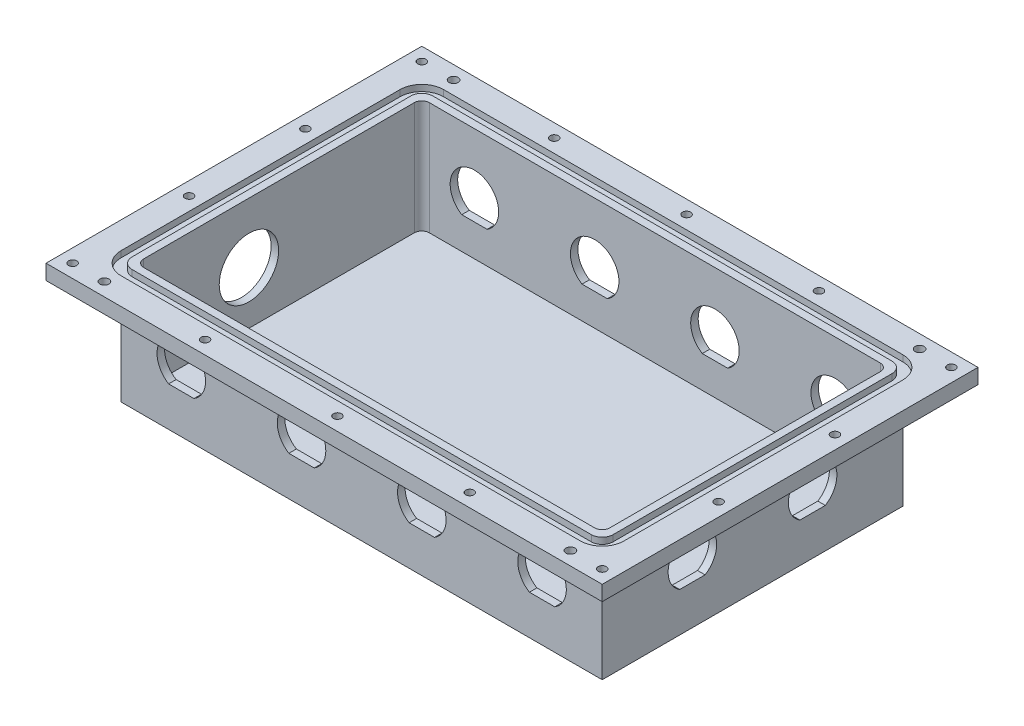
SolidWorks part; units mm, degrees
material "1060 Alloy"
ref_plane "Front Plane" through (0, 0, 0) normal (0, 0, 1) x (1, 0, 0)
ref_plane "Top Plane" through (0, 0, 0) normal (0, 1, 0) x (1, 0, 0)
ref_plane "Right Plane" through (0, 0, 0) normal (1, 0, 0) x (0, 0, -1)
sketch "Sketch1" plane through (0, 0, 0) normal (0, 1, 0) x (1, 0, 0)
  line L1 (101.6, -63.5) -> (-101.6, -63.5)
  line L2 (101.6, -63.5) -> (101.6, 63.5)
  line L3 (101.6, 63.5) -> (-101.6, 63.5)
  line L4 (-101.6, -63.5) -> (-101.6, 63.5)
  line L5 (101.6, -63.5) -> (-101.6, 63.5) construction
  line L6 (101.6, 63.5) -> (-101.6, -63.5) construction
  point P0 (0, 0)
  dimension "D1" = 127
  dimension "D2" = 203.2
extrude "Boss-Extrude1" add sketch "Sketch1" along normal blind 50.8
sketch "Sketch2" plane through (0, 50.8, 0) normal (0, 1, 0) x (1, 0, 0)
  line L8 (-98.425, 60.325) -> (-98.425, -60.325)
  line L9 (98.425, 60.325) -> (-98.425, 60.325)
  line L10 (98.425, -60.325) -> (98.425, 60.325)
  line L11 (-98.425, -60.325) -> (98.425, -60.325)
  line L12 (-98.425, 60.325) -> (-98.425, -60.325)
  line L13 (98.425, 60.325) -> (-98.425, 60.325)
  line L14 (98.425, -60.325) -> (98.425, 60.325)
  line L15 (-98.425, -60.325) -> (98.425, -60.325)
  dimension "D1" = 3.175
extrude "Cut-Extrude1" cut sketch "Sketch2" against normal offset from surface (47.625 mm away) 3.175 up to face at (0, 0, 0)
sketch "Sketch4" plane through (0, 50.8, 0) normal (0, 1, 0) x (1, 0, 0)
  line L0 (-101.6, 63.5) -> (-101.6, -63.5)
  line L1 (-101.6, -63.5) -> (101.6, -63.5)
  line L2 (101.6, -63.5) -> (101.6, 63.5)
  line L3 (101.6, 63.5) -> (-101.6, 63.5)
  line L4 (117.475, 79.375) -> (-117.475, 79.375)
  line L5 (-117.475, 79.375) -> (-117.475, -79.375)
  line L6 (-117.475, -79.375) -> (117.475, -79.375)
  line L7 (117.475, -79.375) -> (117.475, 79.375)
  dimension "D1" = 15.875
extrude "Boss-Extrude2" add sketch "Sketch4" against normal blind 6.35
sketch "Sketch7" plane through (0, 50.8, 0) normal (0, 1, 0) x (1, 0, 0)
  line L4 (-106.2228, 68.1228) -> (-106.2228, -68.1228)
  line L5 (-106.2228, -68.1228) -> (106.2228, -68.1228)
  line L6 (106.2228, -68.1228) -> (106.2228, 68.1228)
  line L7 (106.2228, 68.1228) -> (-106.2228, 68.1228)
  line L8 (-101.6, -63.5) -> (101.6, -63.5)
  line L9 (101.6, -63.5) -> (101.6, 63.5)
  line L10 (101.6, 63.5) -> (-101.6, 63.5)
  line L11 (-101.6, 63.5) -> (-101.6, -63.5)
  line L12 (-101.6, -63.5) -> (101.6, -63.5)
  line L13 (101.6, -63.5) -> (101.6, 63.5)
  line L14 (101.6, 63.5) -> (-101.6, 63.5)
  line L15 (-101.6, 63.5) -> (-101.6, -63.5)
  dimension "D1" = 3.175
  dimension "D2" = 4.6228
extrude "Cut-Extrude2" cut sketch "Sketch7" against normal blind 2.6416
hole_wizard "#8-32 Tapped Hole1" positions "Sketch6" profile "Sketch5" tap size "#8-32" standard "ANSI Inch" end condition through all
sketch "Sketch6" plane through (0, 50.8, 0) normal (0, 1, 0) x (1, 0, 0)
  line L0 (0, 0) -> (0, 79.375) construction
  line L1 (117.475, 79.375) -> (-117.475, 79.375) construction
  line L4 (0, 0) -> (117.475, 0) construction
  line L5 (117.475, -79.375) -> (117.475, 79.375) construction
  line L6 (0, 73.7489) -> (55.9245, 73.7489) construction
  line L7 (55.9245, 73.7489) -> (111.8489, 73.7489) construction
  line L10 (111.8489, 73.7489) -> (111.8489, 24.583) construction
  line L13 (111.8489, 24.583) -> (111.8489, -24.583) construction
  line L16 (106.2228, 68.1228) -> (117.475, 79.375) construction
  point P22 (55.9245, 73.7489)
  point P24 (111.8489, 73.7489)
  point P26 (111.8489, 24.583)
  point P110 (0, 73.7489)
  point P132 (111.8489, -24.583)
  point P133 (111.8489, -73.7489)
  point P134 (55.9245, -73.7489)
  point P135 (0, -73.7489)
  point P145 (-55.9245, -73.7489)
  point P146 (-111.8489, -73.7489)
  point P147 (-111.8489, -24.583)
  point P148 (-111.8489, 24.583)
  point P149 (-111.8489, 73.7489)
  point P150 (-55.9245, 73.7489)
sketch "Sketch5" plane through (55.9245, 50.8, -73.7489) normal (1, 0, 0) x (0, 0, 1)
  line L0 (0, 0) -> (0, 50.8)
  line L1 (0, 50.8) -> (1.7272, 50.8)
  line L2 (1.7272, 50.8) -> (1.7272, 0)
  line L5 (1.7272, 0) -> (0, 0)
  line L11 (0, -6.35) -> (0, 107.95) construction
  dimension "Thread Major Dia." = 3.4544
  dimension "Thru Tap Drill Depth" = 50.8
sketch "O Ring Corner Fillet Dimentions" plane through (0, 50.8, 0) normal (0, 1, 0) x (1, 0, 0)
  line L0 (106.2228, 68.1228) -> (96.9772, 58.8772) construction
  line L1 (106.2228, 68.1228) -> (-106.2228, 68.1228) construction
  line L2 (106.2228, -68.1228) -> (106.2228, 68.1228) construction
  circle A0 centre (96.9772, 58.8772) radius 9.2456
  circle A1 centre (96.9772, 58.8772) radius 4.6228
  dimension "D1" = 4.6228
  dimension "D2" = 18.4912
  dimension "D3" = 9.2456
fillet "Fillet3" radius 4.6228 4 edges at (101.6, 49.4792, 63.5) (-101.6, 49.4792, 63.5) (-101.6, 49.4792, -63.5) (101.6, 49.4792, -63.5)
fillet "Fillet4" radius 9.2456 4 edges at (106.2228, 49.4792, 68.1228) (-106.2228, 49.4792, 68.1228) (-106.2228, 49.4792, -68.1228) (106.2228, 49.4792, -68.1228)
sketch "Sketch10" plane through (0, 0, 63.5) normal (0, 0, 1) x (1, 0, 0)
  line L0 (0, 25.4) -> (50.8, 25.4) construction
  line L1 (-101.6, 0) -> (101.6, 0) construction
  line L3 (-104.775, 16.6624) -> (104.775, 16.6624)
  line L4 (0, 25.4) -> (0, 44.45) construction
  line L5 (-101.6, 44.45) -> (101.6, 44.45) construction
  line L6 (50.8, 25.4) -> (101.6, 25.4) construction
  line L7 (101.6, 44.45) -> (101.6, 0) construction
  line L8 (0, 25.4) -> (-50.8, 25.4) construction
  line L9 (-50.8, 25.4) -> (-101.6, 25.4) construction
  line L10 (-101.6, 44.45) -> (-101.6, 0) construction
  circle A0 centre (-76.2, 25.4) radius 10.2489
  circle A1 centre (-25.4, 25.4) radius 10.2489
  circle A2 centre (25.4, 25.4) radius 10.2489
  circle A3 centre (76.2, 25.4) radius 10.2489
  point P5 (-76.2, 25.4)
  point P9 (-25.4, 25.4)
  point P12 (25.4, 25.4)
  point P13 (76.2, 25.4)
  dimension "D2" = 25.4
  dimension "D1" = 20.4978
  dimension "D3" = 8.7376
extrude "Cut-Extrude5" cut sketch "Sketch10" against normal through all
sketch "Sketch12" plane through (101.6, 0, 0) normal (1, 0, 0) x (0, 0, -1)
  line L0 (63.5, 25.4) -> (-63.5, 25.4) construction
  line L1 (63.5, 44.45) -> (63.5, 0) construction
  line L2 (-63.5, 44.45) -> (-63.5, 0) construction
  line L4 (-63.5, 16.6624) -> (63.5, 16.6624)
  circle A0 centre (-25.4, 25.4) radius 10.2489
  circle A1 centre (25.4, 25.4) radius 10.2489
  point P6 (63.5, 25.4)
  point P7 (-25.4, 25.4)
  point P10 (25.4, 25.4)
  dimension "D2" = 8.7376
  dimension "D3" = 20.4978
  dimension "D1" = 38.1
  dimension "D4" = 38.1
extrude "Cut-Extrude6" cut sketch "Sketch12" against normal up to next
sketch "Sketch13" plane through (-101.6, 0, 0) normal (-1, 0, 0) x (0, 0, 1)
  line L0 (63.5, 22.225) -> (-63.5, 22.225) construction
  line L1 (63.5, 44.45) -> (63.5, 0) construction
  line L2 (-63.5, 44.45) -> (-63.5, 0) construction
  line L3 (-63.5, 44.45) -> (63.5, 44.45) construction
  circle A0 centre (12.7, 25.4) radius 12.554
  point P6 (25.4, 22.225)
  point P7 (12.7, 25.4)
  dimension "D3" = 25.1079
  dimension "D4" = 19.05
  dimension "D5" = 19.05
  dimension "D1" = 38.1
  dimension "D2" = 76.2
extrude "Cut-Extrude7" cut sketch "Sketch13" against normal up to next
fillet "Fillet5" radius 3.175 4 edges at (98.425, 26.9875, -60.325) (-98.425, 26.9875, 60.325) (98.425, 26.9875, 60.325) (-98.425, 26.9875, -60.325)
hole_wizard "#6 Clearance Hole1" positions "Sketch15" profile "Sketch14" hole size "#6" standard "ANSI Inch" end condition through all
sketch "Sketch15" plane through (0, 44.45, 0) normal (0, -1, 0) x (-1, 0, 0)
  line L0 (-101.6, -63.5) -> (-101.6, 63.5) construction
  line L1 (0, 0) -> (0, 87.6055) construction
  line L4 (0, 0) -> (66.1414, 0) construction
  line L7 (-111.8489, 73.7489) -> (-55.9245, 73.7489) construction
  point P2 (-98.425, 73.7489)
  point P31 (-98.425, -73.7489)
  point P32 (98.425, -73.7489)
  point P33 (98.425, 73.7489)
  dimension "D1" = 3.175
sketch "Sketch14" plane through (98.425, 44.45, -73.7489) normal (1, 0, 0) x (0, 0, -1)
  line L0 (0, 0) -> (0, 6.35)
  line L1 (0, 6.35) -> (1.8986, 6.35)
  line L2 (1.8986, 6.35) -> (1.8986, 0)
  line L5 (1.8986, 0) -> (0, 0)
  line L11 (0, -6.35) -> (0, 107.95) construction
  dimension "Thru Hole Dia." = 3.7973
  dimension "Thru Hole Depth" = 6.35
